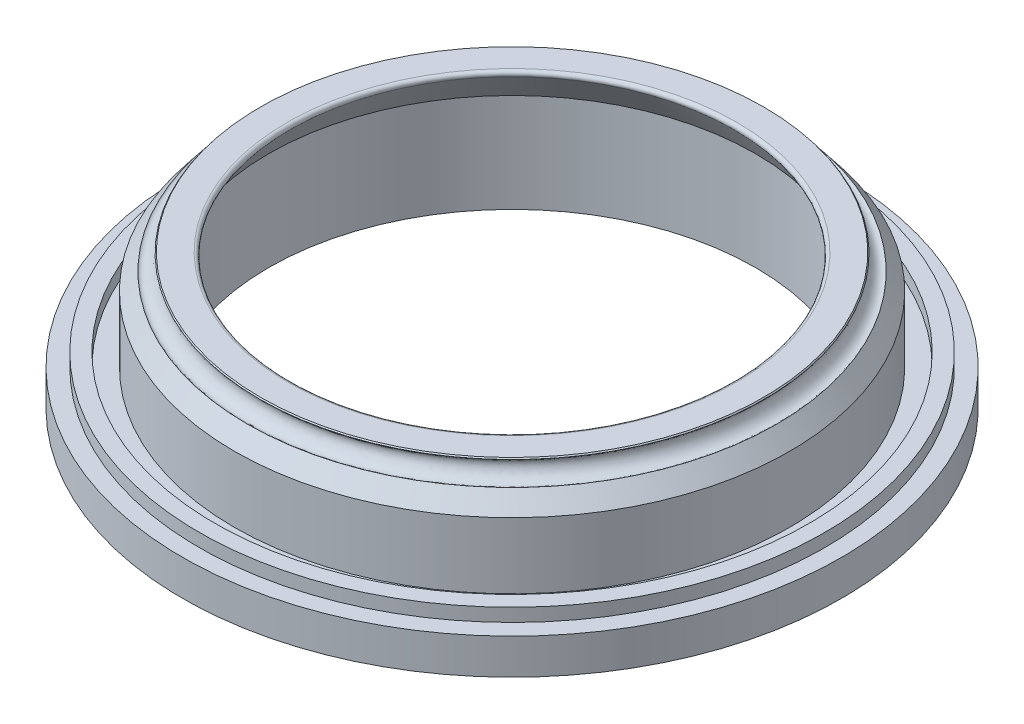
SolidWorks part; units mm, degrees
ref_plane "Front Plane" through (0, 0, 0) normal (0, 0, 1) x (1, 0, 0)
ref_plane "Top Plane" through (0, 0, 0) normal (0, 1, 0) x (1, 0, 0)
ref_plane "Right Plane" through (0, 0, 0) normal (1, 0, 0) x (0, 0, -1)
sketch "Sketch1" plane through (0, 0, 0) normal (0, 0, 1) x (1, 0, 0)
  line L0 (0, 0) -> (0, 38.71) construction
  line L2 (66.3265, 40.7481) -> (76.3265, 40.7481)
  line L3 (76.3265, 40.7481) -> (84.25, 30.5258)
  line L5 (84.25, 10.5258) -> (90.15, 10.5258)
  line L6 (90.15, 10.5258) -> (90.15, 14.5258)
  line L7 (90.15, 14.5258) -> (94.9, 14.5258)
  line L8 (94.9, 14.5258) -> (94.9, 10.5258)
  line L9 (94.9, 10.5258) -> (100, 10.5258)
  line L10 (100, 10.5258) -> (100, -0.2624)
  line L24 (84.25, 30.5258) -> (84.25, 10.5258)
  line L25 (66.3265, 40.7481) -> (73.8722, 29.6747)
  line L27 (73.8722, -0.2624) -> (100, -0.2624)
  line L28 (73.8722, 29.6747) -> (73.8722, -0.2624)
  circle A0 centre (78.7014, -0.7624) radius 2.5 construction
  ellipse E0 centre (78.4366, 38.0258) end of major axis (80.2745, 35.6547) minor radius 2
  ellipse E1 centre (78.7014, -0.2624) end of major axis (75.7014, -0.2624) minor radius 2
  dimension "D18" = 41.0105
  dimension "D25" = 17.9235
  dimension "D16" = 5
  dimension "D1" = 100
  dimension "D2" = 10
  dimension "D3" = 26.1278
  dimension "D4" = 5.9
  dimension "D5" = 4.75
  dimension "D6" = 5.1
  dimension "D7" = 38.71
  dimension "D8" = 10.7881
  dimension "D9" = 40.7481
  dimension "D10" = 4
  dimension "D11" = 37.78
  dimension "D12" = 4.8292
  dimension "D13" = 11.0734
  dimension "D14" = 2
  dimension "D15" = 3
  dimension "D19" = 3
  dimension "D20" = 2
  dimension "D21" = 7.5
revolve "Revolve1" add sketch "Sketch1" angle 360 about L0
sketch "Sketch2" plane through (0, -0.2624, 0) normal (0, -1, 0) x (1, 0, 0)
  circle A0 centre (0, 0) radius 85 construction
  circle A1 centre (0, 85) radius 2.35
  circle A2 centre (0, 0) radius 85 construction
  circle A3 centre (42.5, 73.6122) radius 2.35
  circle A4 centre (0, 0) radius 85 construction
  circle A5 centre (73.6122, 42.5) radius 2.35
  circle A6 centre (0, 0) radius 85 construction
  circle A7 centre (85, 0) radius 2.35
  circle A8 centre (0, 0) radius 85 construction
  circle A9 centre (73.6122, -42.5) radius 2.35
  circle A10 centre (0, 0) radius 85 construction
  circle A11 centre (42.5, -73.6122) radius 2.35
  circle A12 centre (0, 0) radius 85 construction
  circle A13 centre (0, -85) radius 2.35
  circle A14 centre (0, 0) radius 85 construction
  circle A15 centre (-42.5, -73.6122) radius 2.35
  circle A16 centre (0, 0) radius 85 construction
  circle A17 centre (-73.6122, -42.5) radius 2.35
  circle A18 centre (0, 0) radius 85 construction
  circle A19 centre (-85, 0) radius 2.35
  circle A20 centre (0, 0) radius 85 construction
  circle A21 centre (-73.6122, 42.5) radius 2.35
  circle A22 centre (0, 0) radius 85 construction
  circle A23 centre (-42.5, 73.6122) radius 2.35
  point P41 (0, 0)
  dimension "D1" = 170
  dimension "D2" = 4.7
  dimension "D3" = 12
extrude "Cut-Extrude2" cut sketch "Sketch2" against normal blind 5
sketch "Sketch3" plane through (0, -0.2624, 0) normal (0, -1, 0) x (1, 0, 0)
  circle A0 centre (0, 0) radius 100
  circle A1 centre (0, 0) radius 90.5
  dimension "D1" = 181
  dimension "D2" = 200
fillet "Fillet1" radius 1 1 edges at (0, 40.7481, -66.3265)
